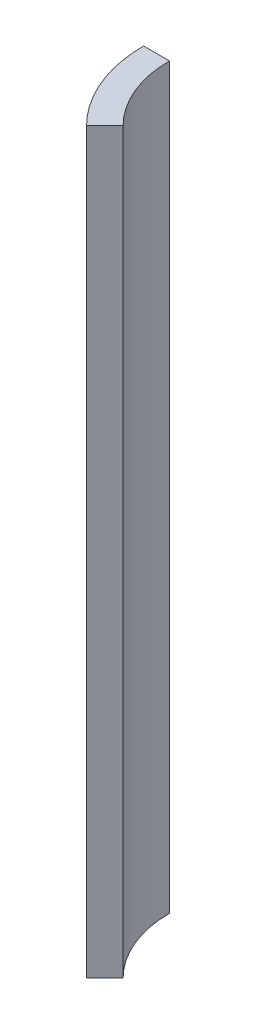
SolidWorks part; units mm, degrees
ref_plane "Front Plane" through (0, 0, 0) normal (0, 0, 1) x (1, 0, 0)
ref_plane "Top Plane" through (0, 0, 0) normal (0, 1, 0) x (1, 0, 0)
ref_plane "Right Plane" through (0, 0, 0) normal (1, 0, 0) x (0, 0, -1)
sketch "Sketch1" plane through (0, 0, 0) normal (0, 1, 0) x (1, 0, 0)
  line L1 (-82.55, 0) -> (-101.6, 0)
  line L2 (-58.3717, -58.3717) -> (-71.842, -71.842)
  arc A0 (-82.55, 0) -> (-58.3717, -58.3717) centre (0, 0) ccw
  arc A1 (-101.6, 0) -> (-71.842, -71.842) centre (0, 0) ccw
  dimension "D1" = 203.2
  dimension "D2" = 165.1
extrude "Boss-Extrude1" add sketch "Sketch1" along normal blind 544.576
